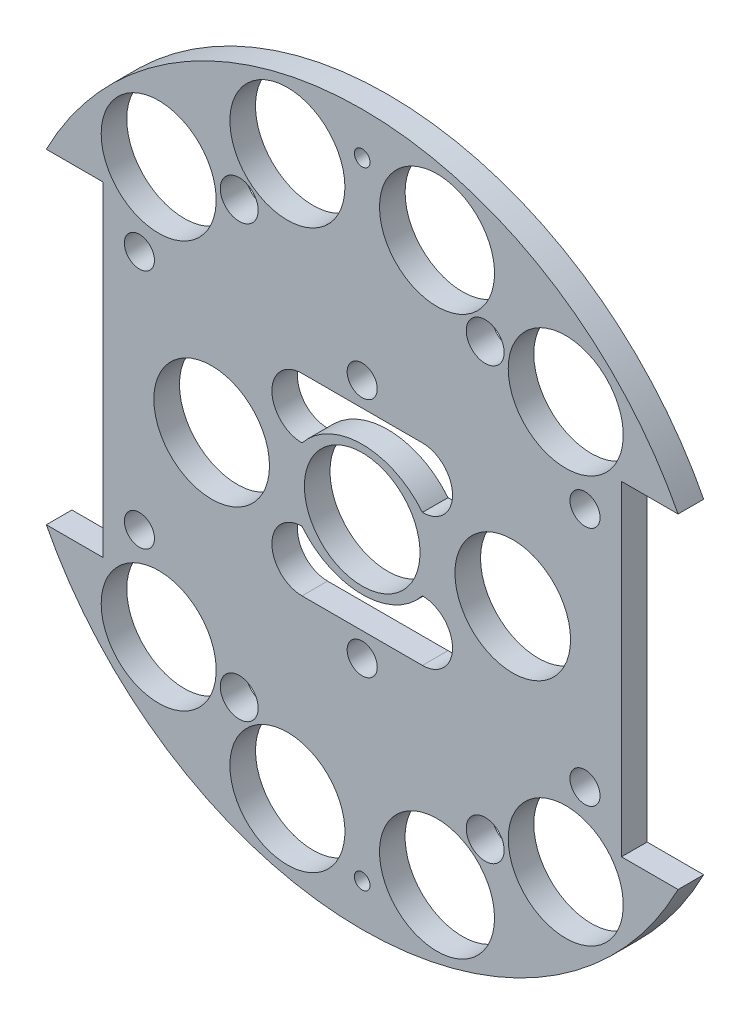
SolidWorks part; units mm, degrees
ref_plane "Front Plane" through (0, 0, 0) normal (0, 0, 1) x (1, 0, 0)
ref_plane "Top Plane" through (0, 0, 0) normal (0, 1, 0) x (1, 0, 0)
ref_plane "Right Plane" through (0, 0, 0) normal (1, 0, 0) x (0, 0, -1)
sketch "Sketch1" plane through (0, 0, 0) normal (0, 0, 1) x (1, 0, 0)
  line L0 (0, 0) -> (-82.1241, 0) construction
  line L1 (0, 0) -> (0, 95.6219) construction
  line L3 (-66.6236, 34.29) -> (-54.6856, 34.29)
  line L5 (-66.6236, -34.29) -> (-54.6856, -34.29)
  line L6 (-54.6856, 34.29) -> (-54.6856, -34.29)
  line L7 (66.6236, -34.29) -> (54.6856, -34.29)
  line L8 (66.6236, 34.29) -> (54.6856, 34.29)
  line L9 (54.6856, 34.29) -> (54.6856, -34.29)
  arc A0 (-66.6236, -34.29) -> (66.6236, -34.29) centre (0, 0) ccw
  circle A1 centre (-45.466, 11.049) radius 1.651
  circle A2 centre (-20.0673, 10.795) radius 1.651
  circle A3 centre (-20.0673, -10.795) radius 1.651
  circle A4 centre (-45.466, -11.049) radius 1.651
  circle A5 centre (45.466, -11.049) radius 1.651
  circle A6 centre (20.0673, -10.795) radius 1.651
  circle A7 centre (20.0673, 10.795) radius 1.651
  circle A8 centre (45.466, 11.049) radius 1.651
  arc A9 (66.6236, 34.29) -> (-66.6236, 34.29) centre (0, 0) ccw
  dimension "D2" = 3.302
  dimension "D3" = 3.302
  dimension "D4" = 25.4
  dimension "D5" = 10.795
  dimension "D10" = 45.466
  dimension "D6" = 68.58
  dimension "D7" = 11.938
  dimension "D8" = 74.93
  dimension "D9" = 74.93
  dimension "D11" = 34.29
extrude "Boss-Extrude2" add sketch "Sketch1" along normal blind 5.3975
sketch "Sketch4" plane through (0, 0, 0) normal (0, 0, -1) x (-1, 0, 0)
  line L1 (51.5324, -18.4451) -> (14.45, -18.4451)
  line L2 (51.5324, -18.4451) -> (51.5324, 15.6028)
  line L3 (51.5324, 15.6028) -> (14.45, 15.6028)
  line L4 (14.45, -18.4451) -> (14.45, 15.6028)
  line L5 (-15.5728, -16.8859) -> (-52.5974, -16.8859)
  line L6 (-15.5728, -16.8859) -> (-15.5728, 15.6028)
  line L7 (-15.5728, 15.6028) -> (-52.5974, 15.6028)
  line L8 (-52.5974, -16.8859) -> (-52.5974, 15.6028)
extrude "Boss-Extrude3" add sketch "Sketch4" against normal up to surface (5.3975 mm away) up to face at (18.4163, 10.795, 5.3975)
sketch "Sketch3" plane through (0, 0, 0) normal (0, 0, -1) x (-1, 0, 0)
  line L0 (0, 0) -> (0, -116.2908) construction
  line L1 (0, 0) -> (-153.8039, 0) construction
  line L2 (15.7776, -58.8828) -> (0, 0) construction
  arc A0 (-66.6236, -34.29) -> (66.6236, -34.29) centre (0, 0) ccw construction
  circle A2 centre (0, 0) radius 12.192
  circle A4 centre (-42.926, -42.926) radius 12.1285
  circle A6 centre (15.7776, -58.8828) radius 12.1285
  circle A7 centre (15.7776, 58.8828) radius 12.1285
  circle A8 centre (-42.926, 42.926) radius 12.1285
  circle A11 centre (42.926, 42.926) radius 12.1285
  circle A12 centre (-15.7776, 58.8828) radius 12.1285
  circle A13 centre (-15.7776, -58.8828) radius 12.1285
  circle A14 centre (42.926, -42.926) radius 12.1285
  point P36 (0, 0)
  point P53 (0, 0)
  point P55 (0, 0)
  dimension "D2" = 42.926
  dimension "D3" = 42.926
  dimension "D4" = 0
  dimension "D5" = 0
  dimension "D6" = 15
  dimension "D10" = 60.96
  dimension "D11" = 24.384
extrude "Cut-Extrude2" cut sketch "Sketch3" against normal through all
extrude "Cut-Extrude4" cut sketch "Sketch6" against normal through all both and the other way through all
sketch "Sketch6" plane through (31.3134, -132.614, 3.175) normal (0, 0, 1) x (0, -1, 0)
  line L0 (-132.614, -31.3134) -> (-132.614, 57.8454) construction
  line L1 (-132.614, -31.3134) -> (-222.516, -31.3134) construction
  circle A0 centre (-158.014, 14.4066) radius 3.175
  circle A1 centre (-173.254, -31.3134) radius 3.175
  circle A3 centre (-158.014, -77.0334) radius 3.175
  circle A4 centre (-107.214, -77.0334) radius 3.175
  circle A5 centre (-91.974, -31.3134) radius 3.175
  circle A6 centre (-107.214, 14.4066) radius 3.175
extrude "Cut-Extrude5" cut sketch "Sketch7" against normal blind 16.51
sketch "Sketch7" plane through (31.3134, -132.559, 15.875) normal (0, 0, 1) x (0, -1, 0)
  line L0 (-132.559, -31.3134) -> (-132.559, -98.8476) construction
  line L1 (-132.559, -31.3134) -> (-20.2053, -31.3134) construction
  circle A1 centre (-198.599, -31.3134) radius 1.651
  circle A2 centre (-66.519, -31.3134) radius 1.651
  circle A3 centre (-132.559, -82.1134) radius 1.651
  circle A4 centre (-132.559, 19.4866) radius 1.651
sketch "Sketch12" plane through (0, 0, 0) normal (0, 0, -1) x (-1, 0, 0)
  line L0 (0, 0) -> (0, 51.8011) construction
  circle A0 centre (25.9376, 45.466) radius 4
  circle A2 centre (15.7776, 58.8828) radius 12.1285 construction
  circle A3 centre (25.9376, -45.466) radius 4
  circle A5 centre (42.926, -42.926) radius 12.1285 construction
  circle A6 centre (-25.9376, 45.466) radius 4
  circle A7 centre (42.926, 42.926) radius 12.1285 construction
  circle A9 centre (-25.9376, -45.466) radius 4
  dimension "D1" = 8
  dimension "D3" = 10.16
  dimension "D4" = 8
  dimension "D5" = 0
  dimension "D6" = 2.54
  dimension "D2" = 2.54
extrude "Cut-Extrude10" cut sketch "Sketch12" against normal blind 83.312
sketch "Sketch15" plane through (0, 0, 0) normal (0, 0, -1) x (-1, 0, 0)
  line L0 (0, 0) -> (91.4732, 0) construction
  circle A0 centre (0, 66.04) radius 1.651
  circle A1 centre (0, -66.04) radius 1.651
  dimension "D1" = 3.302
  dimension "D2" = 66.04
extrude "Cut-Extrude17" cut sketch "Sketch15" against normal blind 83.312
extrude "Cut-Extrude37" cut sketch "Sketch35" against normal blind 48.768 and the other way blind 103.378
sketch "Sketch35" plane through (-30.092, 4.0835, -36.1315) normal (0, 0, 1) x (1, 0, 0)
  line L0 (30.092, -4.0835) -> (148.6336, -4.0835) construction
  line L1 (30.092, -4.0835) -> (30.092, 90.452) construction
  circle A0 centre (-16.898, 21.3165) radius 3.175
  circle A1 centre (77.082, 21.3165) radius 3.175
  circle A2 centre (30.092, 21.3165) radius 3.175
  circle A4 centre (77.082, -29.4835) radius 3.175
  circle A5 centre (30.092, -29.4835) radius 3.175
  circle A6 centre (-16.898, -29.4835) radius 3.175
sketch "Sketch40" plane through (0, 0, 0) normal (0, 0, -1) x (-1, 0, 0)
  line L0 (12.7, -20.32) -> (-12.7, -20.32)
  line L1 (0, 0) -> (-37.8831, 0) construction
  line L2 (12.7, 20.32) -> (-12.7, 20.32)
  arc A0 (12.7, -20.32) -> (12.7, -7.62) centre (12.7, -13.97) ccw
  arc A1 (-12.7, -7.62) -> (-12.7, -20.32) centre (-12.7, -13.97) ccw
  arc A2 (12.7, -7.62) -> (-12.7, -7.62) centre (0, 2.54) cw
  arc A3 (-12.7, 7.62) -> (-12.7, 20.32) centre (-12.7, 13.97) cw
  arc A4 (12.7, 7.62) -> (-12.7, 7.62) centre (0, -2.54) ccw
  arc A5 (12.7, 20.32) -> (12.7, 7.62) centre (12.7, 13.97) cw
  circle A6 centre (-31.75, 0) radius 12.192
  circle A7 centre (31.75, 0) radius 12.192
  dimension "D1" = 12.7
  dimension "D2" = 12.7
  dimension "D7" = 24.384
  dimension "D8" = 24.384
  dimension "D3" = 13.97
  dimension "D4" = 2.54
  dimension "D5" = 25.4
  dimension "D6" = 12.7
  dimension "D9" = 63.5
  dimension "D10" = 31.75
extrude "Cut-Extrude43" cut sketch "Sketch40" against normal blind 25.4
